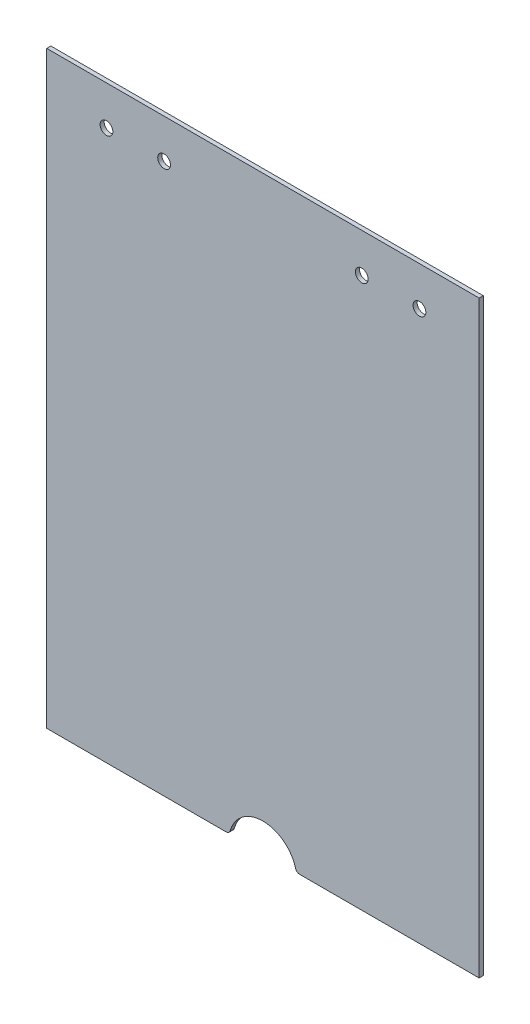
SolidWorks part; units mm, degrees
material "Thornel Mat VMA"
ref_plane "前视基准面" through (0, 0, 0) normal (0, 0, 1) x (1, 0, 0)
ref_plane "上视基准面" through (0, 0, 0) normal (0, 1, 0) x (1, 0, 0)
ref_plane "右视基准面" through (0, 0, 0) normal (1, 0, 0) x (0, 0, -1)
sketch "草图1" plane through (0, 0, 0) normal (0, 0, 1) x (1, 0, 0)
  line L0 (8.9202, -71.5) -> (52.5, -71.5)
  line L1 (-52.5, 71.5) -> (52.5, 71.5)
  line L2 (-52.5, 71.5) -> (-52.5, -71.5)
  line L3 (-52.5, -71.5) -> (-8.9202, -71.5)
  line L4 (52.5, 71.5) -> (52.5, -71.5)
  line L7 (0, 101.3616) -> (0, -109.8062) construction
  circle A1 centre (-38, 62) radius 1.55
  circle A2 centre (-24, 62) radius 1.55
  circle A3 centre (24, 62) radius 1.55
  circle A4 centre (38, 62) radius 1.55
  arc A5 (7.9573, -70.7699) -> (-7.9573, -70.7699) centre (0, -73) ccw
  arc A6 (-8.9202, -71.5) -> (-7.9573, -70.7699) centre (-8.9202, -70.5) ccw
  arc A7 (8.9202, -71.5) -> (7.9573, -70.7699) centre (8.9202, -70.5) cw
  point P0 (0, 0)
  dimension "D10" = 1
  dimension "D11" = 1
  dimension "D1" = 105
  dimension "D2" = 143
  dimension "D4" = 14
  dimension "D5" = 9.5
  dimension "D6" = 9.5
  dimension "D7" = 14.5
  dimension "D8" = 14.5
  dimension "D9" = 9.5
extrude "凸台-拉伸1" add sketch "草图1" along normal blind 1
